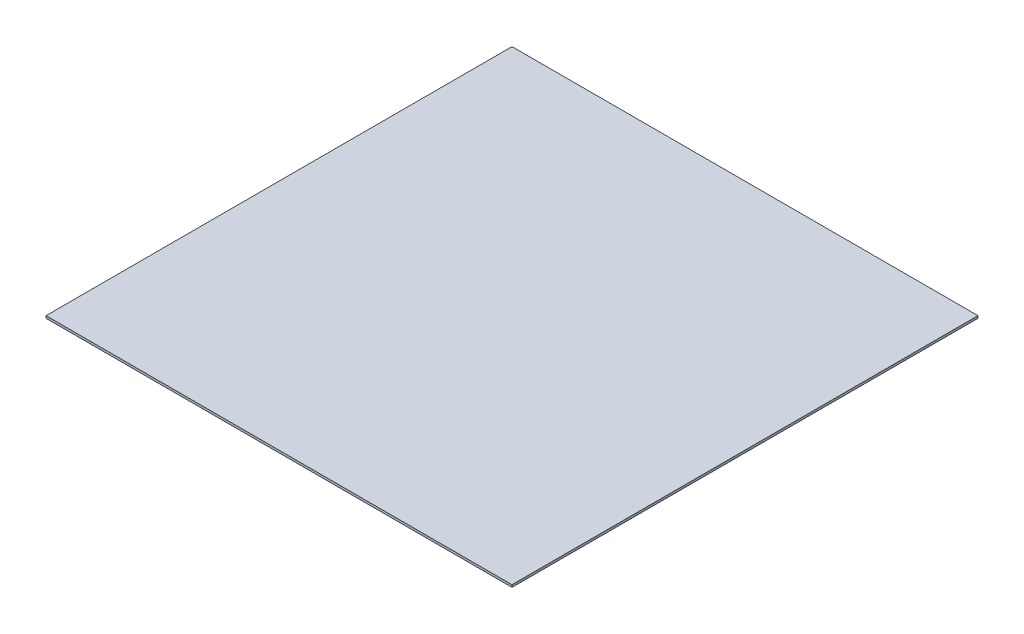
SolidWorks part; units mm, degrees
material "Кремний"
ref_plane "Спереди" through (0, 0, 0) normal (0, 0, 1) x (1, 0, 0)
ref_plane "Сверху" through (0, 0, 0) normal (0, 1, 0) x (1, 0, 0)
ref_plane "Справа" through (0, 0, 0) normal (1, 0, 0) x (0, 0, -1)
sketch "Эскиз1" plane through (0, 0, 0) normal (0, 1, 0) x (1, 0, 0)
  line L1 (-1000, 1000) -> (1000, 1000)
  line L2 (-1000, 1000) -> (-1000, -1000)
  line L3 (-1000, -1000) -> (1000, -1000)
  line L4 (1000, 1000) -> (1000, -1000)
  line L5 (-1000, 1000) -> (1000, -1000) construction
  line L6 (-1000, -1000) -> (1000, 1000) construction
  point P0 (0, 0)
  dimension "D1" = 2000
  dimension "D2" = 2000
extrude "Бобышка-Вытянуть1" add sketch "Эскиз1" along normal blind 10
